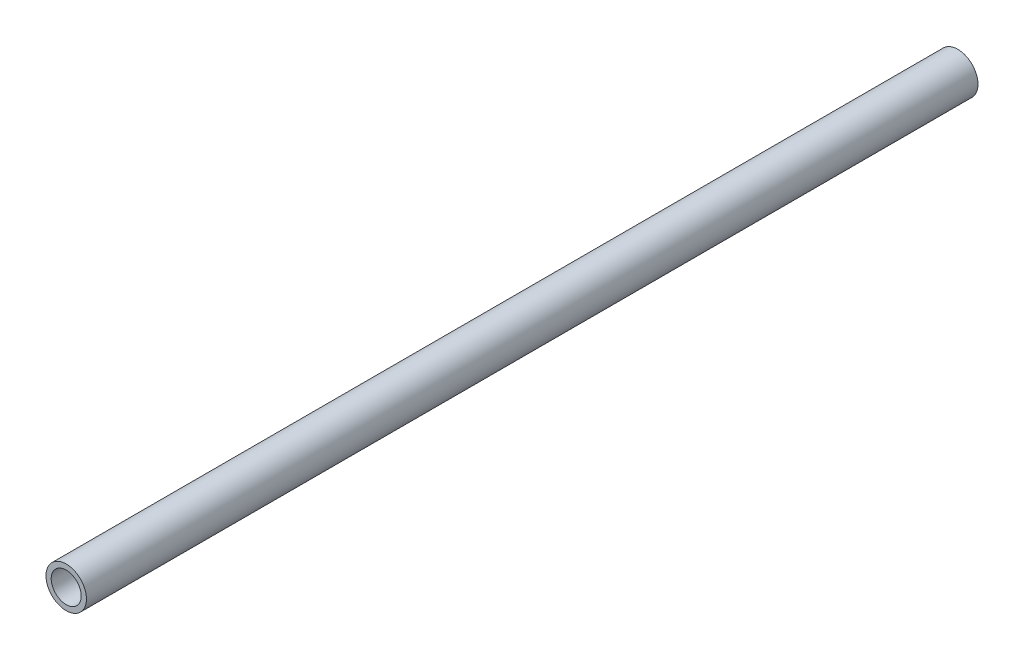
SolidWorks part; units mm, degrees
ref_plane "Front Plane" through (0, 0, 0) normal (0, 0, 1) x (1, 0, 0)
ref_plane "Top Plane" through (0, 0, 0) normal (0, 1, 0) x (1, 0, 0)
ref_plane "Right Plane" through (0, 0, 0) normal (1, 0, 0) x (0, 0, -1)
sketch "Sketch1" plane through (0, 0, 0) normal (0, 0, 1) x (1, 0, 0)
  circle A0 centre (0, 0) radius 10.668
  dimension "Pipe OD" = 21.336
extrude "Extrude-Thin1" add sketch "Sketch1" along normal mid plane 470 thin thin type one direction reverse wall 2.7686
